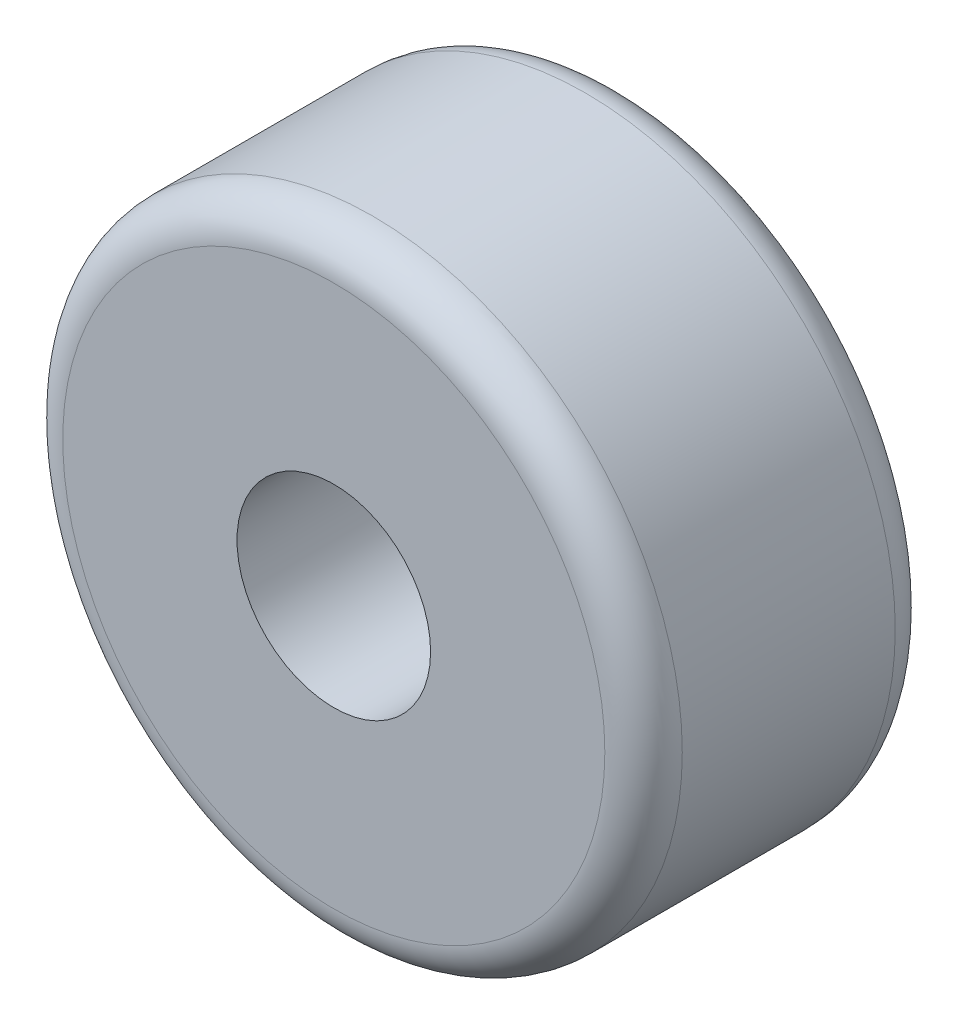
SolidWorks part; units mm, degrees
ref_plane "Plan de face" through (0, 0, 0) normal (0, 0, 1) x (1, 0, 0)
ref_plane "Plan de dessus" through (0, 0, 0) normal (0, 1, 0) x (1, 0, 0)
ref_plane "Plan de droite" through (0, 0, 0) normal (1, 0, 0) x (0, 0, -1)
sketch "Esquisse1" plane through (0, 0, 0) normal (0, 0, 1) x (1, 0, 0)
  circle A0 centre (0, 0) radius 25
  circle A1 centre (0, 0) radius 0.8947
  circle A2 centre (0, 0) radius 80
  dimension "D1" = 50
  dimension "D2" = 160
extrude "Boss.-Extru.1" add sketch "Esquisse1" along normal blind 75 contours A2 A0
fillet "Congé1" radius 10 2 edges at (80, 0, 0) (80, 0, 75)
